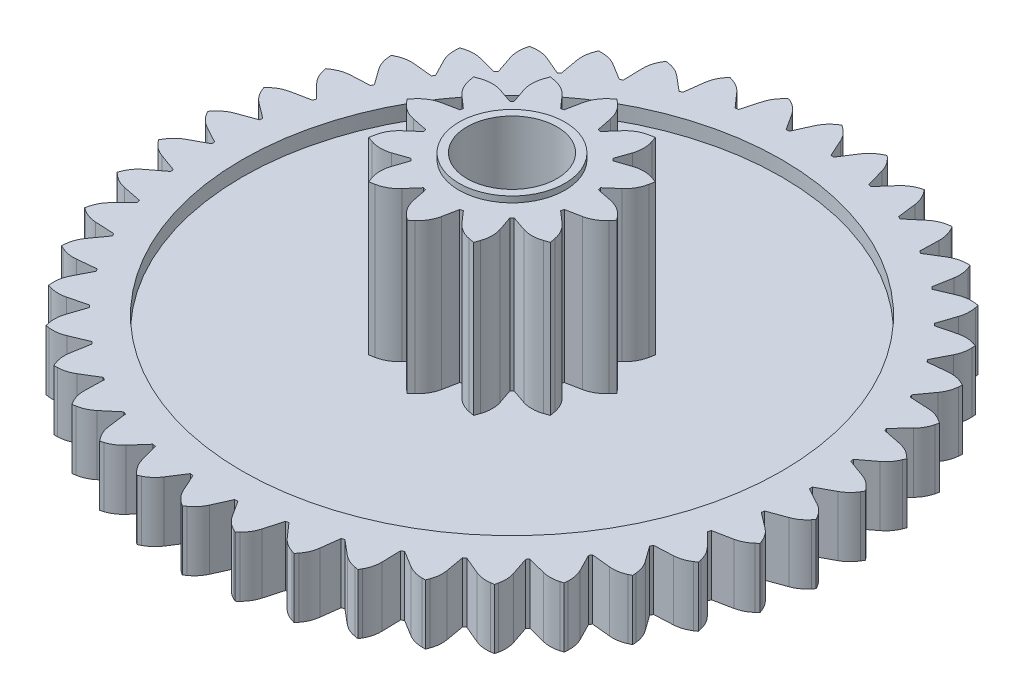
SolidWorks part; units mm, degrees
material "Polyethylene Cross-Linked"
ref_plane "Front Plane" through (0, 0, 0) normal (0, 0, 1) x (1, 0, 0)
ref_plane "Top Plane" through (0, 0, 0) normal (0, 1, 0) x (1, 0, 0)
ref_plane "Right Plane" through (0, 0, 0) normal (1, 0, 0) x (0, 0, -1)
sketch "Sketch1" plane through (0, 0, 0) normal (0, 1, 0) x (1, 0, 0)
  circle A0 centre (0, 0) radius 11
  dimension "D1" = 22
extrude "Boss-Extrude1" add sketch "Sketch1" along normal blind 2
sketch "Sketch2" plane through (0, 2, 0) normal (0, 1, 0) x (1, 0, 0)
  line L0 (0, 0) -> (0, 11) construction
  line L1 (0, 0) -> (1.6395, 10.8771) construction
  line L2 (0, 0) -> (3.2423, 10.5113) construction
  line L3 (0, 0) -> (4.7727, 9.9107) construction
  line L4 (0, 0) -> (6.1965, 9.0886) construction
  line L5 (0, 0) -> (7.4819, 8.0636) construction
  line L6 (0, 0) -> (8.6001, 6.8584) construction
  line L7 (0, 0) -> (9.5263, 5.5) construction
  line L8 (0, 0) -> (10.2396, 4.0188) construction
  line L9 (0, 0) -> (10.7242, 2.4477) construction
  line L10 (0, 0) -> (10.9692, 0.822) construction
  line L11 (0, 0) -> (10.9692, -0.822) construction
  line L12 (0, 0) -> (10.7242, -2.4477) construction
  line L13 (0, 0) -> (10.2396, -4.0188) construction
  line L14 (0, 0) -> (9.5263, -5.5) construction
  line L15 (0, 0) -> (8.6001, -6.8584) construction
  line L16 (0, 0) -> (7.4819, -8.0636) construction
  line L17 (0, 0) -> (6.1965, -9.0886) construction
  line L18 (0, 0) -> (4.7727, -9.9107) construction
  line L19 (0, 0) -> (3.2423, -10.5113) construction
  line L20 (0, 0) -> (1.6395, -10.8771) construction
  line L21 (0, 0) -> (0, -11) construction
  line L22 (0, 0) -> (-1.6395, -10.8771) construction
  line L23 (0, 0) -> (-3.2423, -10.5113) construction
  line L24 (0, 0) -> (-4.7727, -9.9107) construction
  line L25 (0, 0) -> (-6.1965, -9.0886) construction
  line L26 (0, 0) -> (-7.4819, -8.0636) construction
  line L27 (0, 0) -> (-8.6001, -6.8584) construction
  line L28 (0, 0) -> (-9.5263, -5.5) construction
  line L29 (0, 0) -> (-10.2396, -4.0188) construction
  line L30 (0, 0) -> (-10.7242, -2.4477) construction
  line L31 (0, 0) -> (-10.9692, -0.822) construction
  line L32 (0, 0) -> (-10.9692, 0.822) construction
  line L33 (0, 0) -> (-10.7242, 2.4477) construction
  line L34 (0, 0) -> (-10.2396, 4.0188) construction
  line L35 (0, 0) -> (-9.5263, 5.5) construction
  line L36 (0, 0) -> (-8.6001, 6.8584) construction
  line L37 (0, 0) -> (-7.4819, 8.0636) construction
  line L38 (0, 0) -> (-6.1965, 9.0886) construction
  line L39 (0, 0) -> (-4.7727, 9.9107) construction
  line L40 (0, 0) -> (-3.2423, 10.5113) construction
  line L41 (0, 0) -> (-1.6395, 10.8771) construction
  line L42 (0, 11) -> (1.6395, 10.8771) construction
  line L43 (0.8197, 10.9386) -> (0.745, 9.9414) construction
  line L44 (0.7949, 9.9376) -> (0.6951, 9.9451)
  line L45 (0.6951, 9.9451) -> (0.4343, 10.5244)
  line L46 (0.0948, 10.9339) -> (0, 11)
  line L47 (0.7949, 9.9376) -> (1.1391, 10.4716)
  line L48 (1.5359, 10.8259) -> (1.6395, 10.8771)
  line L49 (1.7233, 10.7976) -> (1.6395, 10.8771)
  line L50 (2.1696, 9.7304) -> (1.998, 10.3421)
  line L51 (2.2671, 9.7082) -> (2.1696, 9.7304)
  line L52 (2.2671, 9.7082) -> (2.6871, 10.1848)
  line L53 (3.1322, 10.476) -> (3.2423, 10.5113)
  line L54 (3.3134, 10.4202) -> (3.2423, 10.5113)
  line L55 (3.5956, 9.2984) -> (3.5171, 9.9288)
  line L56 (3.6887, 9.2618) -> (3.5956, 9.2984)
  line L57 (3.6887, 9.2618) -> (4.1751, 9.6706)
  line L58 (4.6586, 9.8922) -> (4.7727, 9.9107)
  line L59 (4.8294, 9.8099) -> (4.7727, 9.9107)
  line L60 (4.9413, 8.6586) -> (4.9576, 9.2937)
  line L61 (5.0279, 8.6086) -> (4.9413, 8.6586)
  line L62 (5.0279, 8.6086) -> (5.5698, 8.9403)
  line L63 (6.081, 9.0874) -> (6.1965, 9.0886)
  line L64 (6.2376, 8.9806) -> (6.1965, 9.0886)
  line L65 (6.1766, 7.8254) -> (6.2874, 8.451)
  line L66 (6.2548, 7.7631) -> (6.1766, 7.8254)
  line L67 (6.2548, 7.7631) -> (6.8401, 8.0103)
  line L68 (7.3674, 8.0795) -> (7.4819, 8.0636)
  line L69 (7.5064, 7.9506) -> (7.4819, 8.0636)
  line L70 (7.274, 6.8175) -> (7.4768, 7.4195)
  line L71 (7.342, 6.7442) -> (7.274, 6.8175)
  line L72 (7.342, 6.7442) -> (7.9575, 6.9014)
  line L73 (8.4893, 6.8912) -> (8.6001, 6.8584)
  line L74 (8.6075, 6.7431) -> (8.6001, 6.8584)
  line L75 (8.2088, 5.6572) -> (8.4991, 6.2223)
  line L76 (8.2651, 5.5746) -> (8.2088, 5.6572)
  line L77 (8.2651, 5.5746) -> (8.8973, 5.6383)
  line L78 (9.4216, 5.549) -> (9.5263, 5.5)
  line L79 (9.5164, 5.3849) -> (9.5263, 5.5)
  line L80 (8.9603, 4.3705) -> (9.3315, 4.8861)
  line L81 (9.0037, 4.2804) -> (8.9603, 4.3705)
  line L82 (9.0037, 4.2804) -> (9.6382, 4.2493)
  line L83 (10.1434, 4.0828) -> (10.2396, 4.0188)
  line L84 (10.2127, 3.9064) -> (10.2396, 4.0188)
  line L85 (9.5116, 2.9863) -> (9.9556, 3.4407)
  line L86 (9.5411, 2.8907) -> (9.5116, 2.9863)
  line L87 (9.5411, 2.8907) -> (10.1639, 2.7653)
  line L88 (10.6386, 2.5254) -> (10.7242, 2.4477)
  line L89 (10.6808, 2.3406) -> (10.7242, 2.4477)
  line L90 (9.8504, 1.5353) -> (10.3572, 1.9185)
  line L91 (9.8653, 1.4364) -> (9.8504, 1.5353)
  line L92 (9.8653, 1.4364) -> (10.4625, 1.2196)
  line L93 (10.8962, 0.9116) -> (10.9692, 0.822)
  line L94 (10.9104, 0.7226) -> (10.9692, 0.822)
  line L95 (9.9692, 0.05) -> (10.5274, 0.3534)
  line L96 (9.9692, -0.05) -> (9.9692, 0.05)
  line L97 (9.9692, -0.05) -> (10.5274, -0.3534)
  line L98 (10.9104, -0.7226) -> (10.9692, -0.822)
  line L99 (10.8962, -0.9116) -> (10.9692, -0.822)
  line L100 (9.8653, -1.4364) -> (10.4625, -1.2196)
  line L101 (9.8504, -1.5353) -> (9.8653, -1.4364)
  line L102 (9.8504, -1.5353) -> (10.3572, -1.9185)
  line L103 (10.6808, -2.3406) -> (10.7242, -2.4477)
  line L104 (10.6386, -2.5254) -> (10.7242, -2.4477)
  line L105 (9.5411, -2.8907) -> (10.1639, -2.7653)
  line L106 (9.5116, -2.9863) -> (9.5411, -2.8907)
  line L107 (9.5116, -2.9863) -> (9.9556, -3.4407)
  line L108 (10.2127, -3.9064) -> (10.2396, -4.0188)
  line L109 (10.1434, -4.0828) -> (10.2396, -4.0188)
  line L110 (9.0037, -4.2804) -> (9.6382, -4.2493)
  line L111 (8.9603, -4.3705) -> (9.0037, -4.2804)
  line L112 (8.9603, -4.3705) -> (9.3315, -4.8861)
  line L113 (9.5164, -5.3849) -> (9.5263, -5.5)
  line L114 (9.4216, -5.549) -> (9.5263, -5.5)
  line L115 (8.2651, -5.5746) -> (8.8973, -5.6383)
  line L116 (8.2088, -5.6572) -> (8.2651, -5.5746)
  line L117 (8.2088, -5.6572) -> (8.4991, -6.2223)
  line L118 (8.6075, -6.7431) -> (8.6001, -6.8584)
  line L119 (8.4893, -6.8912) -> (8.6001, -6.8584)
  line L120 (7.342, -6.7442) -> (7.9575, -6.9014)
  line L121 (7.274, -6.8175) -> (7.342, -6.7442)
  line L122 (7.274, -6.8175) -> (7.4768, -7.4195)
  line L123 (7.5064, -7.9506) -> (7.4819, -8.0636)
  line L124 (7.3674, -8.0795) -> (7.4819, -8.0636)
  line L125 (6.2548, -7.7631) -> (6.8401, -8.0103)
  line L126 (6.1766, -7.8254) -> (6.2548, -7.7631)
  line L127 (6.1766, -7.8254) -> (6.2874, -8.451)
  line L128 (6.2376, -8.9806) -> (6.1965, -9.0886)
  line L129 (6.081, -9.0874) -> (6.1965, -9.0886)
  line L130 (5.0279, -8.6086) -> (5.5698, -8.9403)
  line L131 (4.9413, -8.6586) -> (5.0279, -8.6086)
  line L132 (4.9413, -8.6586) -> (4.9576, -9.2937)
  line L133 (4.8294, -9.8099) -> (4.7727, -9.9107)
  line L134 (4.6586, -9.8922) -> (4.7727, -9.9107)
  line L135 (3.6887, -9.2618) -> (4.1751, -9.6706)
  line L136 (3.5956, -9.2984) -> (3.6887, -9.2618)
  line L137 (3.5956, -9.2984) -> (3.5171, -9.9288)
  line L138 (3.3134, -10.4202) -> (3.2423, -10.5113)
  line L139 (3.1322, -10.476) -> (3.2423, -10.5113)
  line L140 (2.2671, -9.7082) -> (2.6871, -10.1848)
  line L141 (2.1696, -9.7304) -> (2.2671, -9.7082)
  line L142 (2.1696, -9.7304) -> (1.998, -10.3421)
  line L143 (1.7233, -10.7976) -> (1.6395, -10.8771)
  line L144 (1.5359, -10.8259) -> (1.6395, -10.8771)
  line L145 (0.7949, -9.9376) -> (1.1391, -10.4716)
  line L146 (0.6951, -9.9451) -> (0.7949, -9.9376)
  line L147 (0.6951, -9.9451) -> (0.4343, -10.5244)
  line L148 (0.0948, -10.9339) -> (0, -11)
  line L149 (-0.0948, -10.9339) -> (0, -11)
  line L150 (-0.6951, -9.9451) -> (-0.4343, -10.5244)
  line L151 (-0.7949, -9.9376) -> (-0.6951, -9.9451)
  line L152 (-0.7949, -9.9376) -> (-1.1391, -10.4716)
  line L153 (-1.5359, -10.8259) -> (-1.6395, -10.8771)
  line L154 (-1.7233, -10.7976) -> (-1.6395, -10.8771)
  line L155 (-2.1696, -9.7304) -> (-1.998, -10.3421)
  line L156 (-2.2671, -9.7082) -> (-2.1696, -9.7304)
  line L157 (-2.2671, -9.7082) -> (-2.6871, -10.1848)
  line L158 (-3.1322, -10.476) -> (-3.2423, -10.5113)
  line L159 (-3.3134, -10.4202) -> (-3.2423, -10.5113)
  line L160 (-3.5956, -9.2984) -> (-3.5171, -9.9288)
  line L161 (-3.6887, -9.2618) -> (-3.5956, -9.2984)
  line L162 (-3.6887, -9.2618) -> (-4.1751, -9.6706)
  line L163 (-4.6586, -9.8922) -> (-4.7727, -9.9107)
  line L164 (-4.8294, -9.8099) -> (-4.7727, -9.9107)
  line L165 (-4.9413, -8.6586) -> (-4.9576, -9.2937)
  line L166 (-5.0279, -8.6086) -> (-4.9413, -8.6586)
  line L167 (-5.0279, -8.6086) -> (-5.5698, -8.9403)
  line L168 (-6.081, -9.0874) -> (-6.1965, -9.0886)
  line L169 (-6.2376, -8.9806) -> (-6.1965, -9.0886)
  line L170 (-6.1766, -7.8254) -> (-6.2874, -8.451)
  line L171 (-6.2548, -7.7631) -> (-6.1766, -7.8254)
  line L172 (-6.2548, -7.7631) -> (-6.8401, -8.0103)
  line L173 (-7.3674, -8.0795) -> (-7.4819, -8.0636)
  line L174 (-7.5064, -7.9506) -> (-7.4819, -8.0636)
  line L175 (-7.274, -6.8175) -> (-7.4768, -7.4195)
  line L176 (-7.342, -6.7442) -> (-7.274, -6.8175)
  line L177 (-7.342, -6.7442) -> (-7.9575, -6.9014)
  line L178 (-8.4893, -6.8912) -> (-8.6001, -6.8584)
  line L179 (-8.6075, -6.7431) -> (-8.6001, -6.8584)
  line L180 (-8.2088, -5.6572) -> (-8.4991, -6.2223)
  line L181 (-8.2651, -5.5746) -> (-8.2088, -5.6572)
  line L182 (-8.2651, -5.5746) -> (-8.8973, -5.6383)
  line L183 (-9.4216, -5.549) -> (-9.5263, -5.5)
  line L184 (-9.5164, -5.3849) -> (-9.5263, -5.5)
  line L185 (-8.9603, -4.3705) -> (-9.3315, -4.8861)
  line L186 (-9.0037, -4.2804) -> (-8.9603, -4.3705)
  line L187 (-9.0037, -4.2804) -> (-9.6382, -4.2493)
  line L188 (-10.1434, -4.0828) -> (-10.2396, -4.0188)
  line L189 (-10.2127, -3.9064) -> (-10.2396, -4.0188)
  line L190 (-9.5116, -2.9863) -> (-9.9556, -3.4407)
  line L191 (-9.5411, -2.8907) -> (-9.5116, -2.9863)
  line L192 (-9.5411, -2.8907) -> (-10.1639, -2.7653)
  line L193 (-10.6386, -2.5254) -> (-10.7242, -2.4477)
  line L194 (-10.6808, -2.3406) -> (-10.7242, -2.4477)
  line L195 (-9.8504, -1.5353) -> (-10.3572, -1.9185)
  line L196 (-9.8653, -1.4364) -> (-9.8504, -1.5353)
  line L197 (-9.8653, -1.4364) -> (-10.4625, -1.2196)
  line L198 (-10.8962, -0.9116) -> (-10.9692, -0.822)
  line L199 (-10.9104, -0.7226) -> (-10.9692, -0.822)
  line L200 (-9.9692, -0.05) -> (-10.5274, -0.3534)
  line L201 (-9.9692, 0.05) -> (-9.9692, -0.05)
  line L202 (-9.9692, 0.05) -> (-10.5274, 0.3534)
  line L203 (-10.9104, 0.7226) -> (-10.9692, 0.822)
  line L204 (-10.8962, 0.9116) -> (-10.9692, 0.822)
  line L205 (-9.8653, 1.4364) -> (-10.4625, 1.2196)
  line L206 (-9.8504, 1.5353) -> (-9.8653, 1.4364)
  line L207 (-9.8504, 1.5353) -> (-10.3572, 1.9185)
  line L208 (-10.6808, 2.3406) -> (-10.7242, 2.4477)
  line L209 (-10.6386, 2.5254) -> (-10.7242, 2.4477)
  line L210 (-9.5411, 2.8907) -> (-10.1639, 2.7653)
  line L211 (-9.5116, 2.9863) -> (-9.5411, 2.8907)
  line L212 (-9.5116, 2.9863) -> (-9.9556, 3.4407)
  line L213 (-10.2127, 3.9064) -> (-10.2396, 4.0188)
  line L214 (-10.1434, 4.0828) -> (-10.2396, 4.0188)
  line L215 (-9.0037, 4.2804) -> (-9.6382, 4.2493)
  line L216 (-8.9603, 4.3705) -> (-9.0037, 4.2804)
  line L217 (-8.9603, 4.3705) -> (-9.3315, 4.8861)
  line L218 (-9.5164, 5.3849) -> (-9.5263, 5.5)
  line L219 (-9.4216, 5.549) -> (-9.5263, 5.5)
  line L220 (-8.2651, 5.5746) -> (-8.8973, 5.6383)
  line L221 (-8.2088, 5.6572) -> (-8.2651, 5.5746)
  line L222 (-8.2088, 5.6572) -> (-8.4991, 6.2223)
  line L223 (-8.6075, 6.7431) -> (-8.6001, 6.8584)
  line L224 (-8.4893, 6.8912) -> (-8.6001, 6.8584)
  line L225 (-7.342, 6.7442) -> (-7.9575, 6.9014)
  line L226 (-7.274, 6.8175) -> (-7.342, 6.7442)
  line L227 (-7.274, 6.8175) -> (-7.4768, 7.4195)
  line L228 (-7.5064, 7.9506) -> (-7.4819, 8.0636)
  line L229 (-7.3674, 8.0795) -> (-7.4819, 8.0636)
  line L230 (-6.2548, 7.7631) -> (-6.8401, 8.0103)
  line L231 (-6.1766, 7.8254) -> (-6.2548, 7.7631)
  line L232 (-6.1766, 7.8254) -> (-6.2874, 8.451)
  line L233 (-6.2376, 8.9806) -> (-6.1965, 9.0886)
  line L234 (-6.081, 9.0874) -> (-6.1965, 9.0886)
  line L235 (-5.0279, 8.6086) -> (-5.5698, 8.9403)
  line L236 (-4.9413, 8.6586) -> (-5.0279, 8.6086)
  line L237 (-4.9413, 8.6586) -> (-4.9576, 9.2937)
  line L238 (-4.8294, 9.8099) -> (-4.7727, 9.9107)
  line L239 (-4.6586, 9.8922) -> (-4.7727, 9.9107)
  line L240 (-3.6887, 9.2618) -> (-4.1751, 9.6706)
  line L241 (-3.5956, 9.2984) -> (-3.6887, 9.2618)
  line L242 (-3.5956, 9.2984) -> (-3.5171, 9.9288)
  line L243 (-3.3134, 10.4202) -> (-3.2423, 10.5113)
  line L244 (-3.1322, 10.476) -> (-3.2423, 10.5113)
  line L245 (-2.2671, 9.7082) -> (-2.6871, 10.1848)
  line L246 (-2.1696, 9.7304) -> (-2.2671, 9.7082)
  line L247 (-2.1696, 9.7304) -> (-1.998, 10.3421)
  line L248 (-1.7233, 10.7976) -> (-1.6395, 10.8771)
  line L249 (-1.5359, 10.8259) -> (-1.6395, 10.8771)
  line L250 (-0.7949, 9.9376) -> (-1.1391, 10.4716)
  line L251 (-0.6951, 9.9451) -> (-0.7949, 9.9376)
  line L252 (-0.6951, 9.9451) -> (-0.4343, 10.5244)
  line L253 (-0.0948, 10.9339) -> (0, 11)
  circle A0 centre (0, 0) radius 11 construction
  arc A1 (0.4343, 10.5244) -> (0.0948, 10.9339) centre (-0.4775, 10.1138) ccw
  arc A2 (1.1391, 10.4716) -> (1.5359, 10.8259) centre (1.9796, 9.9297) cw
  arc A3 (1.998, 10.3421) -> (1.7233, 10.7976) centre (1.0352, 10.072) ccw
  arc A4 (2.6871, 10.1848) -> (3.1322, 10.476) centre (3.4374, 9.5237) cw
  arc A5 (3.5171, 9.9288) -> (3.3134, 10.4202) centre (2.5248, 9.8052) ccw
  arc A6 (4.1751, 9.6706) -> (4.6586, 9.8922) centre (4.8185, 8.905) cw
  arc A7 (4.9576, 9.2937) -> (4.8294, 9.8099) centre (3.958, 9.3194) ccw
  arc A8 (5.5698, 8.9403) -> (6.081, 9.0874) centre (6.0919, 8.0874) cw
  arc A9 (6.2874, 8.451) -> (6.2376, 8.9806) centre (5.3028, 8.6254) ccw
  arc A10 (6.8401, 8.0103) -> (7.3674, 8.0795) centre (7.2292, 7.0891) cw
  arc A11 (7.4768, 7.4195) -> (7.5064, 7.9506) centre (6.5291, 7.7388) ccw
  arc A12 (7.9575, 6.9014) -> (8.4893, 6.8912) centre (8.205, 5.9325) cw
  arc A13 (8.4991, 6.2223) -> (8.6075, 6.7431) centre (7.6096, 6.6792) ccw
  arc A14 (8.8973, 5.6383) -> (9.4216, 5.549) centre (8.9976, 4.6434) cw
  arc A15 (9.3315, 4.8861) -> (9.5164, 5.3849) centre (8.5201, 5.4705) ccw
  arc A16 (9.6382, 4.2493) -> (10.1434, 4.0828) centre (9.5892, 3.2505) cw
  arc A17 (9.9556, 3.4407) -> (10.2127, 3.9064) centre (9.2402, 4.1395) ccw
  arc A18 (10.1639, 2.7653) -> (10.6386, 2.5254) centre (9.9665, 1.785) cw
  arc A19 (10.3572, 1.9185) -> (10.6808, 2.3406) centre (9.754, 2.7161) ccw
  arc A20 (10.4625, 1.2196) -> (10.8962, 0.9116) centre (10.1212, 0.2796) cw
  arc A21 (10.5274, 0.3534) -> (10.9104, 0.7226) centre (10.0499, 1.232) ccw
  arc A22 (10.5274, -0.3534) -> (10.9104, -0.7226) centre (10.0499, -1.232) cw
  arc A23 (10.4625, -1.2196) -> (10.8962, -0.9116) centre (10.1212, -0.2796) ccw
  arc A24 (10.3572, -1.9185) -> (10.6808, -2.3406) centre (9.754, -2.7161) cw
  arc A25 (10.1639, -2.7653) -> (10.6386, -2.5254) centre (9.9665, -1.785) ccw
  arc A26 (9.9556, -3.4407) -> (10.2127, -3.9064) centre (9.2402, -4.1395) cw
  arc A27 (9.6382, -4.2493) -> (10.1434, -4.0828) centre (9.5892, -3.2505) ccw
  arc A28 (9.3315, -4.8861) -> (9.5164, -5.3849) centre (8.5201, -5.4705) cw
  arc A29 (8.8973, -5.6383) -> (9.4216, -5.549) centre (8.9976, -4.6434) ccw
  arc A30 (8.4991, -6.2223) -> (8.6075, -6.7431) centre (7.6096, -6.6792) cw
  arc A31 (7.9575, -6.9014) -> (8.4893, -6.8912) centre (8.205, -5.9325) ccw
  arc A32 (7.4768, -7.4195) -> (7.5064, -7.9506) centre (6.5291, -7.7388) cw
  arc A33 (6.8401, -8.0103) -> (7.3674, -8.0795) centre (7.2292, -7.0891) ccw
  arc A34 (6.2874, -8.451) -> (6.2376, -8.9806) centre (5.3028, -8.6254) cw
  arc A35 (5.5698, -8.9403) -> (6.081, -9.0874) centre (6.0919, -8.0874) ccw
  arc A36 (4.9576, -9.2937) -> (4.8294, -9.8099) centre (3.958, -9.3194) cw
  arc A37 (4.1751, -9.6706) -> (4.6586, -9.8922) centre (4.8185, -8.905) ccw
  arc A38 (3.5171, -9.9288) -> (3.3134, -10.4202) centre (2.5248, -9.8052) cw
  arc A39 (2.6871, -10.1848) -> (3.1322, -10.476) centre (3.4374, -9.5237) ccw
  arc A40 (1.998, -10.3421) -> (1.7233, -10.7976) centre (1.0352, -10.072) cw
  arc A41 (1.1391, -10.4716) -> (1.5359, -10.8259) centre (1.9796, -9.9297) ccw
  arc A42 (0.4343, -10.5244) -> (0.0948, -10.9339) centre (-0.4775, -10.1138) cw
  arc A43 (-0.4343, -10.5244) -> (-0.0948, -10.9339) centre (0.4775, -10.1138) ccw
  arc A44 (-1.1391, -10.4716) -> (-1.5359, -10.8259) centre (-1.9796, -9.9297) cw
  arc A45 (-1.998, -10.3421) -> (-1.7233, -10.7976) centre (-1.0352, -10.072) ccw
  arc A46 (-2.6871, -10.1848) -> (-3.1322, -10.476) centre (-3.4374, -9.5237) cw
  arc A47 (-3.5171, -9.9288) -> (-3.3134, -10.4202) centre (-2.5248, -9.8052) ccw
  arc A48 (-4.1751, -9.6706) -> (-4.6586, -9.8922) centre (-4.8185, -8.905) cw
  arc A49 (-4.9576, -9.2937) -> (-4.8294, -9.8099) centre (-3.958, -9.3194) ccw
  arc A50 (-5.5698, -8.9403) -> (-6.081, -9.0874) centre (-6.0919, -8.0874) cw
  arc A51 (-6.2874, -8.451) -> (-6.2376, -8.9806) centre (-5.3028, -8.6254) ccw
  arc A52 (-6.8401, -8.0103) -> (-7.3674, -8.0795) centre (-7.2292, -7.0891) cw
  arc A53 (-7.4768, -7.4195) -> (-7.5064, -7.9506) centre (-6.5291, -7.7388) ccw
  arc A54 (-7.9575, -6.9014) -> (-8.4893, -6.8912) centre (-8.205, -5.9325) cw
  arc A55 (-8.4991, -6.2223) -> (-8.6075, -6.7431) centre (-7.6096, -6.6792) ccw
  arc A56 (-8.8973, -5.6383) -> (-9.4216, -5.549) centre (-8.9976, -4.6434) cw
  arc A57 (-9.3315, -4.8861) -> (-9.5164, -5.3849) centre (-8.5201, -5.4705) ccw
  arc A58 (-9.6382, -4.2493) -> (-10.1434, -4.0828) centre (-9.5892, -3.2505) cw
  arc A59 (-9.9556, -3.4407) -> (-10.2127, -3.9064) centre (-9.2402, -4.1395) ccw
  arc A60 (-10.1639, -2.7653) -> (-10.6386, -2.5254) centre (-9.9665, -1.785) cw
  arc A61 (-10.3572, -1.9185) -> (-10.6808, -2.3406) centre (-9.754, -2.7161) ccw
  arc A62 (-10.4625, -1.2196) -> (-10.8962, -0.9116) centre (-10.1212, -0.2796) cw
  arc A63 (-10.5274, -0.3534) -> (-10.9104, -0.7226) centre (-10.0499, -1.232) ccw
  arc A64 (-10.5274, 0.3534) -> (-10.9104, 0.7226) centre (-10.0499, 1.232) cw
  arc A65 (-10.4625, 1.2196) -> (-10.8962, 0.9116) centre (-10.1212, 0.2796) ccw
  arc A66 (-10.3572, 1.9185) -> (-10.6808, 2.3406) centre (-9.754, 2.7161) cw
  arc A67 (-10.1639, 2.7653) -> (-10.6386, 2.5254) centre (-9.9665, 1.785) ccw
  arc A68 (-9.9556, 3.4407) -> (-10.2127, 3.9064) centre (-9.2402, 4.1395) cw
  arc A69 (-9.6382, 4.2493) -> (-10.1434, 4.0828) centre (-9.5892, 3.2505) ccw
  arc A70 (-9.3315, 4.8861) -> (-9.5164, 5.3849) centre (-8.5201, 5.4705) cw
  arc A71 (-8.8973, 5.6383) -> (-9.4216, 5.549) centre (-8.9976, 4.6434) ccw
  arc A72 (-8.4991, 6.2223) -> (-8.6075, 6.7431) centre (-7.6096, 6.6792) cw
  arc A73 (-7.9575, 6.9014) -> (-8.4893, 6.8912) centre (-8.205, 5.9325) ccw
  arc A74 (-7.4768, 7.4195) -> (-7.5064, 7.9506) centre (-6.5291, 7.7388) cw
  arc A75 (-6.8401, 8.0103) -> (-7.3674, 8.0795) centre (-7.2292, 7.0891) ccw
  arc A76 (-6.2874, 8.451) -> (-6.2376, 8.9806) centre (-5.3028, 8.6254) cw
  arc A77 (-5.5698, 8.9403) -> (-6.081, 9.0874) centre (-6.0919, 8.0874) ccw
  arc A78 (-4.9576, 9.2937) -> (-4.8294, 9.8099) centre (-3.958, 9.3194) cw
  arc A79 (-4.1751, 9.6706) -> (-4.6586, 9.8922) centre (-4.8185, 8.905) ccw
  arc A80 (-3.5171, 9.9288) -> (-3.3134, 10.4202) centre (-2.5248, 9.8052) cw
  arc A81 (-2.6871, 10.1848) -> (-3.1322, 10.476) centre (-3.4374, 9.5237) ccw
  arc A82 (-1.998, 10.3421) -> (-1.7233, 10.7976) centre (-1.0352, 10.072) cw
  arc A83 (-1.1391, 10.4716) -> (-1.5359, 10.8259) centre (-1.9796, 9.9297) ccw
  arc A84 (-0.4343, 10.5244) -> (-0.0948, 10.9339) centre (0.4775, 10.1138) cw
  dimension "D4" = 1
  dimension "D2" = 1
  dimension "D3" = 0.05
  dimension "D1" = 42
  dimension "D5" = 42
extrude "Cut-Extrude1" cut sketch "Sketch2" against normal blind 2 flip side to cut
sketch "Sketch3" plane through (0, 2, 0) normal (0, 1, 0) x (1, 0, 0)
  circle A0 centre (0, 0) radius 9
  dimension "D1" = 18
extrude "Cut-Extrude2" cut sketch "Sketch3" against normal blind 0.5
sketch "Sketch4" plane through (0, 0, 0) normal (0, -1, 0) x (1, 0, 0)
  circle A0 centre (0, 0) radius 9
  circle A1 centre (0, 0) radius 6.5
  circle A2 centre (0, 0) radius 6
  dimension "D1" = 13
  dimension "D2" = 12
extrude "Cut-Extrude3" cut sketch "Sketch4" against normal blind 0.5 contours A0 A1 | A2
fillet "Fillet1" radius 0.2 2 edges at (0, 0, -6.5) (0, 0, -6)
sketch "Sketch5" plane through (0, 1.5, 0) normal (0, 1, 0) x (1, 0, 0)
  line L0 (0, 0) -> (0, 3.5) construction
  line L1 (0, 0) -> (1.75, 3.0311) construction
  line L2 (0, 0) -> (3.0311, 1.75) construction
  line L3 (0, 0) -> (3.5, 0) construction
  line L4 (0, 0) -> (3.0311, -1.75) construction
  line L5 (0, 0) -> (1.75, -3.0311) construction
  line L6 (0, 0) -> (0, -3.5) construction
  line L7 (0, 0) -> (-1.75, -3.0311) construction
  line L8 (0, 0) -> (-3.0311, -1.75) construction
  line L9 (0, 0) -> (-3.5, 0) construction
  line L10 (0, 0) -> (-3.0311, 1.75) construction
  line L11 (0, 0) -> (-1.75, 3.0311) construction
  line L12 (0, 3.5) -> (1.75, 3.0311) construction
  line L13 (0.875, 3.2655) -> (0.6162, 2.2996) construction
  line L14 (0.6645, 2.2867) -> (0.5679, 2.3126)
  line L15 (0.5679, 2.3126) -> (0.4678, 2.8168)
  line L16 (0.1394, 3.38) -> (0, 3.5)
  line L17 (0.6645, 2.2867) -> (1.0033, 2.6734)
  line L18 (1.5693, 2.9969) -> (1.75, 3.0311)
  line L19 (1.8107, 2.8575) -> (1.75, 3.0311)
  line L20 (1.6481, 1.7188) -> (1.8135, 2.2056)
  line L21 (1.7188, 1.6481) -> (1.6481, 1.7188)
  line L22 (1.7188, 1.6481) -> (2.2056, 1.8135)
  line L23 (2.8575, 1.8107) -> (3.0311, 1.75)
  line L24 (2.9969, 1.5693) -> (3.0311, 1.75)
  line L25 (2.2867, 0.6645) -> (2.6734, 1.0033)
  line L26 (2.3126, 0.5679) -> (2.2867, 0.6645)
  line L27 (2.3126, 0.5679) -> (2.8168, 0.4678)
  line L28 (3.38, 0.1394) -> (3.5, 0)
  line L29 (3.38, -0.1394) -> (3.5, 0)
  line L30 (2.3126, -0.5679) -> (2.8168, -0.4678)
  line L31 (2.2867, -0.6645) -> (2.3126, -0.5679)
  line L32 (2.2867, -0.6645) -> (2.6734, -1.0033)
  line L33 (2.9969, -1.5693) -> (3.0311, -1.75)
  line L34 (2.8575, -1.8107) -> (3.0311, -1.75)
  line L35 (1.7188, -1.6481) -> (2.2056, -1.8135)
  line L36 (1.6481, -1.7188) -> (1.7188, -1.6481)
  line L37 (1.6481, -1.7188) -> (1.8135, -2.2056)
  line L38 (1.8107, -2.8575) -> (1.75, -3.0311)
  line L39 (1.5693, -2.9969) -> (1.75, -3.0311)
  line L40 (0.6645, -2.2867) -> (1.0033, -2.6734)
  line L41 (0.5679, -2.3126) -> (0.6645, -2.2867)
  line L42 (0.5679, -2.3126) -> (0.4678, -2.8168)
  line L43 (0.1394, -3.38) -> (0, -3.5)
  line L44 (-0.1394, -3.38) -> (0, -3.5)
  line L45 (-0.5679, -2.3126) -> (-0.4678, -2.8168)
  line L46 (-0.6645, -2.2867) -> (-0.5679, -2.3126)
  line L47 (-0.6645, -2.2867) -> (-1.0033, -2.6734)
  line L48 (-1.5693, -2.9969) -> (-1.75, -3.0311)
  line L49 (-1.8107, -2.8575) -> (-1.75, -3.0311)
  line L50 (-1.6481, -1.7188) -> (-1.8135, -2.2056)
  line L51 (-1.7188, -1.6481) -> (-1.6481, -1.7188)
  line L52 (-1.7188, -1.6481) -> (-2.2056, -1.8135)
  line L53 (-2.8575, -1.8107) -> (-3.0311, -1.75)
  line L54 (-2.9969, -1.5693) -> (-3.0311, -1.75)
  line L55 (-2.2867, -0.6645) -> (-2.6734, -1.0033)
  line L56 (-2.3126, -0.5679) -> (-2.2867, -0.6645)
  line L57 (-2.3126, -0.5679) -> (-2.8168, -0.4678)
  line L58 (-3.38, -0.1394) -> (-3.5, 0)
  line L59 (-3.38, 0.1394) -> (-3.5, 0)
  line L60 (-2.3126, 0.5679) -> (-2.8168, 0.4678)
  line L61 (-2.2867, 0.6645) -> (-2.3126, 0.5679)
  line L62 (-2.2867, 0.6645) -> (-2.6734, 1.0033)
  line L63 (-2.9969, 1.5693) -> (-3.0311, 1.75)
  line L64 (-2.8575, 1.8107) -> (-3.0311, 1.75)
  line L65 (-1.7188, 1.6481) -> (-2.2056, 1.8135)
  line L66 (-1.6481, 1.7188) -> (-1.7188, 1.6481)
  line L67 (-1.6481, 1.7188) -> (-1.8135, 2.2056)
  line L68 (-1.8107, 2.8575) -> (-1.75, 3.0311)
  line L69 (-1.5693, 2.9969) -> (-1.75, 3.0311)
  line L70 (-0.6645, 2.2867) -> (-1.0033, 2.6734)
  line L71 (-0.5679, 2.3126) -> (-0.6645, 2.2867)
  line L72 (-0.5679, 2.3126) -> (-0.4678, 2.8168)
  line L73 (-0.1394, 3.38) -> (0, 3.5)
  arc A1 (0.4678, 2.8168) -> (0.1394, 3.38) centre (-0.5131, 2.6222) ccw
  arc A2 (1.0033, 2.6734) -> (1.5693, 2.9969) centre (1.7554, 2.0143) cw
  arc A3 (1.8135, 2.2056) -> (1.8107, 2.8575) centre (0.8668, 2.5274) ccw
  arc A4 (2.2056, 1.8135) -> (2.8575, 1.8107) centre (2.5274, 0.8668) cw
  arc A5 (2.6734, 1.0033) -> (2.9969, 1.5693) centre (2.0143, 1.7554) ccw
  arc A6 (2.8168, 0.4678) -> (3.38, 0.1394) centre (2.6222, -0.5131) cw
  arc A7 (2.8168, -0.4678) -> (3.38, -0.1394) centre (2.6222, 0.5131) ccw
  arc A8 (2.6734, -1.0033) -> (2.9969, -1.5693) centre (2.0143, -1.7554) cw
  arc A9 (2.2056, -1.8135) -> (2.8575, -1.8107) centre (2.5274, -0.8668) ccw
  arc A10 (1.8135, -2.2056) -> (1.8107, -2.8575) centre (0.8668, -2.5274) cw
  arc A11 (1.0033, -2.6734) -> (1.5693, -2.9969) centre (1.7554, -2.0143) ccw
  arc A12 (0.4678, -2.8168) -> (0.1394, -3.38) centre (-0.5131, -2.6222) cw
  arc A13 (-0.4678, -2.8168) -> (-0.1394, -3.38) centre (0.5131, -2.6222) ccw
  arc A14 (-1.0033, -2.6734) -> (-1.5693, -2.9969) centre (-1.7554, -2.0143) cw
  arc A15 (-1.8135, -2.2056) -> (-1.8107, -2.8575) centre (-0.8668, -2.5274) ccw
  arc A16 (-2.2056, -1.8135) -> (-2.8575, -1.8107) centre (-2.5274, -0.8668) cw
  arc A17 (-2.6734, -1.0033) -> (-2.9969, -1.5693) centre (-2.0143, -1.7554) ccw
  arc A18 (-2.8168, -0.4678) -> (-3.38, -0.1394) centre (-2.6222, 0.5131) cw
  arc A19 (-2.8168, 0.4678) -> (-3.38, 0.1394) centre (-2.6222, -0.5131) ccw
  arc A20 (-2.6734, 1.0033) -> (-2.9969, 1.5693) centre (-2.0143, 1.7554) cw
  arc A21 (-2.2056, 1.8135) -> (-2.8575, 1.8107) centre (-2.5274, 0.8668) ccw
  arc A22 (-1.8135, 2.2056) -> (-1.8107, 2.8575) centre (-0.8668, 2.5274) cw
  arc A23 (-1.0033, 2.6734) -> (-1.5693, 2.9969) centre (-1.7554, 2.0143) ccw
  arc A24 (-0.4678, 2.8168) -> (-0.1394, 3.38) centre (0.5131, 2.6222) cw
  dimension "D5" = 1
  dimension "D3" = 1
  dimension "D4" = 0.05
  dimension "D2" = 12
  dimension "D6" = 12
extrude "Boss-Extrude2" add sketch "Sketch5" along normal blind 5
sketch "Sketch6" plane through (0, 6.5, 0) normal (0, 1, 0) x (1, 0, 0)
  circle A0 centre (0, 0) radius 1.5
  dimension "D1" = 3
extrude "Cut-Extrude4" cut sketch "Sketch6" against normal through all
sketch "Sketch7" plane through (0, 6.5, 0) normal (0, 1, 0) x (1, 0, 0)
  circle A0 centre (0, 0) radius 1.5
  circle A1 centre (0, 0) radius 1.7691
extrude "Boss-Extrude3" add sketch "Sketch7" along normal blind 0.2
